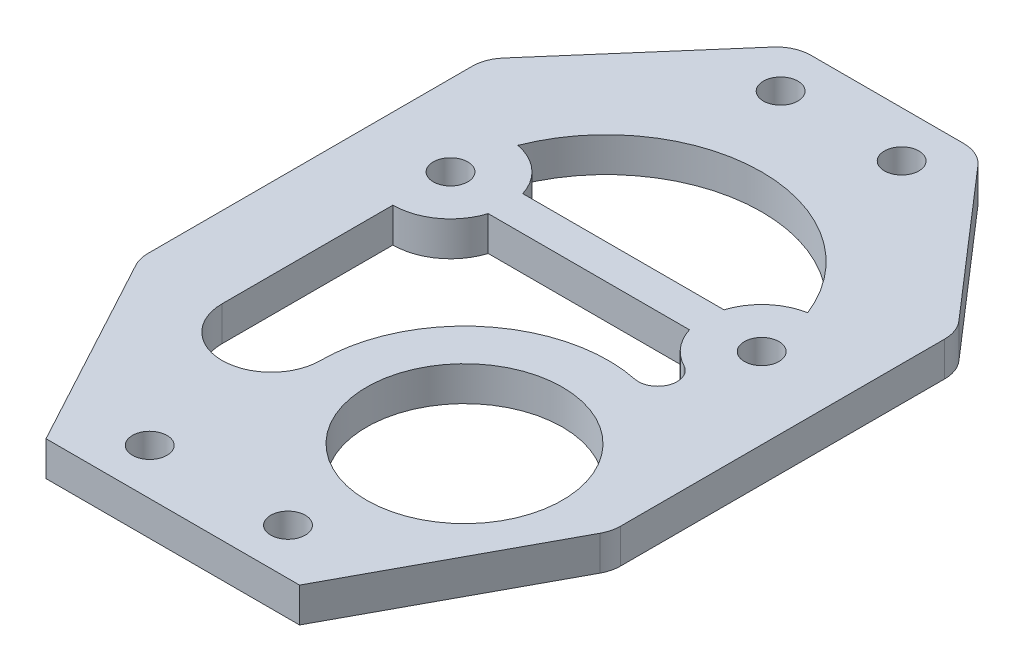
SolidWorks part; units mm, degrees
ref_plane "Front" through (0, 0, 0) normal (0, 0, 1) x (1, 0, 0)
ref_plane "Top" through (0, 0, 0) normal (0, 1, 0) x (1, 0, 0)
ref_plane "Right" through (0, 0, 0) normal (1, 0, 0) x (0, 0, -1)
sketch "Sketch1" plane through (0, 0, 0) normal (0, 1, 0) x (1, 0, 0)
  line L0 (0, 24.4003) -> (0, 0) construction
  line L1 (0, 0) -> (-13.5, 0) construction
  line L2 (8, 24.4003) -> (-8, 24.4003)
  line L3 (-8, 24.4003) -> (-20.5, 10)
  line L4 (-20.5, 10) -> (-20.5, -20)
  line L5 (-20.5, -20) -> (-11, -37.5997)
  line L6 (-11, -37.5997) -> (11, -37.5997)
  line L7 (20.5, -20) -> (11, -37.5997)
  line L8 (20.5, 10) -> (20.5, -20)
  line L9 (8, 24.4003) -> (20.5, 10)
  line L11 (7.5302, -19.8174) -> (17.65, -25.2799) construction
  line L12 (-13.5, -5) -> (-13.5, -19.8174)
  line L13 (8.7303, -1.5) -> (-8.7303, -1.5)
  line L15 (8.7303, 1.5) -> (-8.7303, 1.5)
  line L17 (8.7303, -1.5) -> (-8.7303, 1.5) construction
  line L18 (8.7303, 1.5) -> (-8.7303, -1.5) construction
  arc A0 (12.5741, 4.9135) -> (-12.5741, 4.9135) centre (0, 0) ccw
  circle A1 centre (-5.25, 20.3945) radius 1.5
  circle A2 centre (-6, -33.5997) radius 1.5
  circle A3 centre (6, -33.5997) radius 1.5
  circle A4 centre (5.25, 20.3945) radius 1.5
  arc A5 (-13.5, -5) -> (-8.7303, -1.5) centre (-13.5, 0) ccw
  arc A6 (8.7303, -1.5) -> (11.188, -4.4333) centre (13.5, 0) ccw
  circle A7 centre (-13.5, 0) radius 1.5
  circle A8 centre (13.5, 0) radius 1.5
  arc A9 (-13.5, -19.8174) -> (-4.9698, -19.8174) centre (-9.2349, -19.8174) ccw
  arc A10 (-4.9698, -19.8174) -> (10.0668, -7.5775) centre (7.5302, -19.8174) cw
  arc A11 (10.0668, -7.5775) -> (11.188, -4.4333) centre (10.4088, -5.9275) ccw
  circle A12 centre (7.5302, -19.8174) radius 8.5
  arc A13 (-8.7303, 1.5) -> (-12.5741, 4.9135) centre (-13.5, 0) ccw
  arc A14 (12.5741, 4.9135) -> (8.7303, 1.5) centre (13.5, 0) ccw
  point P15 (0, -37.5997)
  dimension "D5" = 3
  dimension "D6" = 4
  dimension "D7" = 10.5
  dimension "D8" = 3
  dimension "D10" = 17
  dimension "D15" = 4
  dimension "D16" = 10
  dimension "D17" = 13.5
  dimension "D18" = 3
  dimension "D19" = 3
  dimension "D23" = 12
  dimension "D24" = 22
  dimension "D1" = 62
  dimension "D2" = 41
  dimension "D3" = 16
  dimension "D4" = 22
  dimension "D9" = 11.5
  dimension "D11" = 6
  dimension "D12" = 20
  dimension "D13" = 30
  dimension "D14" = 10
  dimension "D20" = 3
  dimension "D21" = 45
  dimension "D22" = 13.5
extrude "Boss-Extrude1" add sketch "Sketch1" along normal mid plane 3
fillet "Fillet1" radius 3 6 edges at (-20.5, 0, 20) (-20.5, 0, -10) (-8, 0, -24.4003) (8, 0, -24.4003) (20.5, 0, -10) (20.5, 0, 20)
